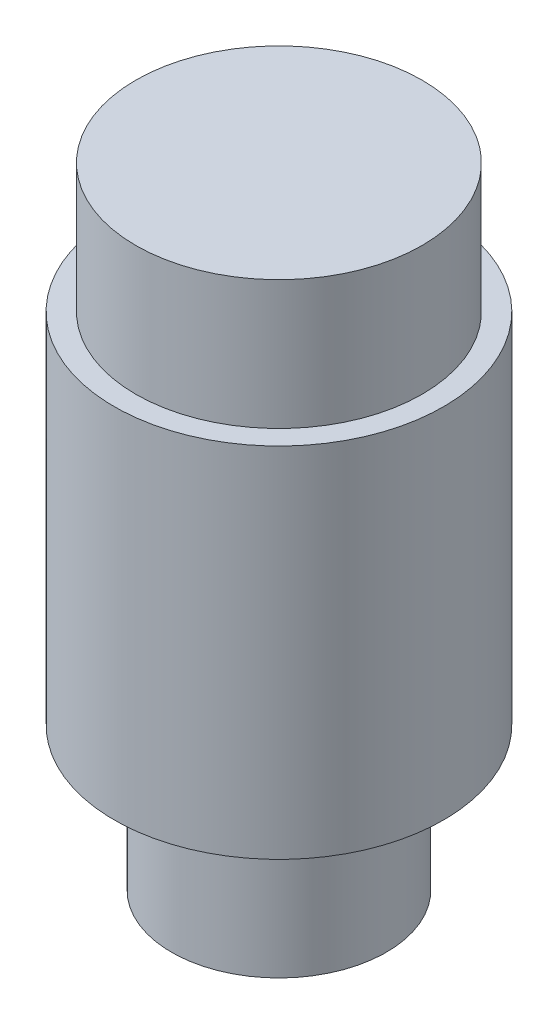
SolidWorks part; units mm, degrees
ref_plane "前视基准面" through (0, 0, 0) normal (0, 0, 1) x (1, 0, 0)
ref_plane "上视基准面" through (0, 0, 0) normal (0, 1, 0) x (1, 0, 0)
ref_plane "右视基准面" through (0, 0, 0) normal (1, 0, 0) x (0, 0, -1)
sketch "草图1" plane through (0, 0, 0) normal (0, 0, 1) x (1, 0, 0)
  line L0 (0, 0) -> (10, 0)
  line L1 (10, 0) -> (10, -9)
  line L2 (11.5, -34) -> (7.5, -34)
  line L3 (7.5, -34) -> (7.5, -44)
  line L4 (7.5, -44) -> (0, -44)
  line L5 (0, -44) -> (0, 0)
  line L6 (10, -9) -> (11.5, -9)
  line L7 (11.5, -9) -> (11.5, -34)
  dimension "D1" = 10
  dimension "D2" = 7.5
  dimension "D3" = 11.5
  dimension "D4" = 44
  dimension "D5" = 34
  dimension "D6" = 25
revolve "旋转1" add sketch "草图1" angle 360 about L5
